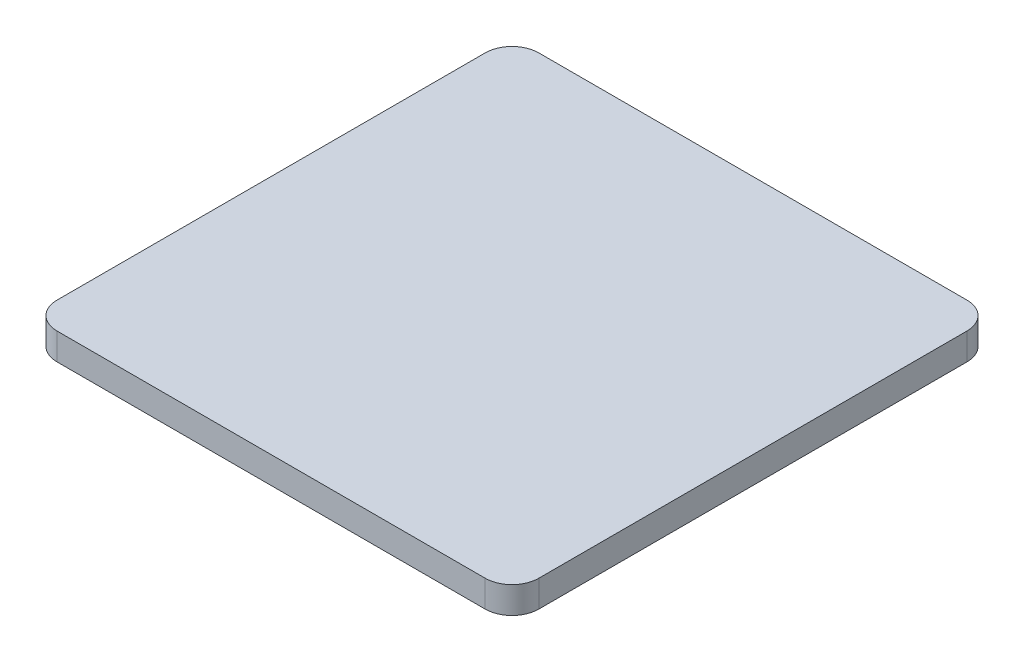
SolidWorks part; units mm, degrees
ref_plane "Plano frontal" through (0, 0, 0) normal (0, 0, 1) x (1, 0, 0)
ref_plane "Plano superior" through (0, 0, 0) normal (0, 1, 0) x (1, 0, 0)
ref_plane "Plano direito" through (0, 0, 0) normal (1, 0, 0) x (0, 0, -1)
sketch "Esboço1" plane through (0, 0, 0) normal (0, 1, 0) x (1, 0, 0)
  line L1 (-80, -90) -> (80, -90)
  line L2 (-90, -80) -> (-90, 80)
  line L3 (-80, 90) -> (80, 90)
  line L4 (90, -80) -> (90, 80)
  line L5 (-90, -90) -> (90, 90) construction
  line L6 (-90, 90) -> (90, -90) construction
  arc A0 (-80, -90) -> (-90, -80) centre (-80, -80) cw
  arc A1 (80, -90) -> (90, -80) centre (80, -80) ccw
  arc A2 (80, 90) -> (90, 80) centre (80, 80) cw
  arc A3 (-90, 80) -> (-80, 90) centre (-80, 80) cw
  point P0 (0, 0)
  dimension "D3" = 10
  dimension "D1" = 180
  dimension "D2" = 180
extrude "Ressalto-extrusão1" add sketch "Esboço1" along normal blind 10
